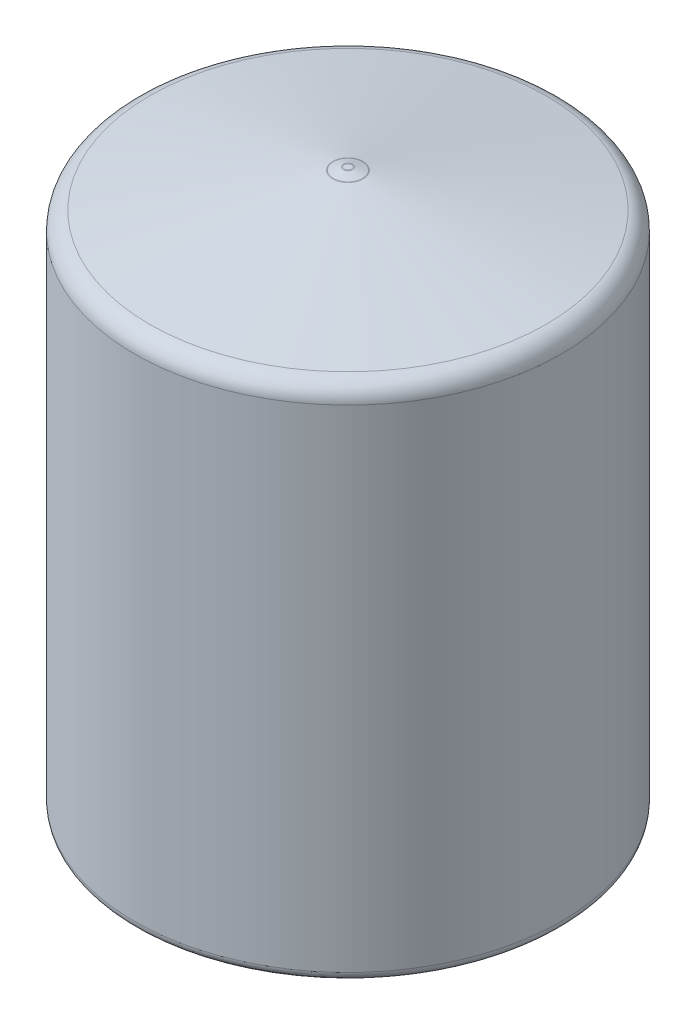
SolidWorks part; units mm, degrees
material "PE High Density"
ref_plane "Front Plane" through (0, 0, 0) normal (0, 0, 1) x (1, 0, 0)
ref_plane "Top Plane" through (0, 0, 0) normal (0, 1, 0) x (1, 0, 0)
ref_plane "Right Plane" through (0, 0, 0) normal (1, 0, 0) x (0, 0, -1)
sketch "Sketch1" plane through (0, 0, 0) normal (0, 0, 1) x (1, 0, 0)
  line L0 (10, 0) -> (10, 26.5856)
  line L1 (10.6855, 27.9826) -> (0.8, 29.849)
  line L2 (11.5, 0) -> (11.5, 27)
  line L3 (0, 30) -> (0, 29.5)
  line L4 (10, 26.5856) -> (1.2654, 28.2346)
  line L5 (0.2509, 29.9934) -> (0.8, 29.849)
  line L6 (0.2, 30) -> (0, 30)
  line L7 (10, 0) -> (11.5, 0)
  line L8 (0, 9.5) -> (0, 0) construction
  line L9 (0, 29.5) -> (1.2654, 28.2346)
  line L10 (0, 30) -> (-6.88, 27.1682) construction
  line L11 (0.1592, 28.4434) -> (-6.3091, 25.7811) construction
  line L12 (11.5, 27.8289) -> (0, 30) construction
  line L13 (10, 26.5856) -> (0.1592, 28.4434) construction
  line L14 (11.5, 0) -> (11.5, 27.8289) construction
  arc A0 (11.5, 27) -> (10.6855, 27.9826) centre (10.5, 27) ccw
  arc A1 (0.2509, 29.9934) -> (0.2, 30) centre (0.2, 29.8) ccw
  point P12 (0.794, 29.8501)
  point P22 (0, 0)
  point P23 (0, 0)
  point P24 (0, 0)
  point P25 (1.1903, 29.8)
  point P26 (0.7827, 29.8501)
  dimension "D5" = 1
  dimension "D3" = 0.2
  dimension "D1" = 1.5
  dimension "D2" = 23
  dimension "D4" = 30
  dimension "D6" = 27
  dimension "D7" = 0.5
  dimension "D8" = 0.2
  dimension "D9" = 45
  dimension "D10" = 0.8
revolve "Revolve1" add sketch "Sketch1" angle 360 about L8
fillet "Fillet1" radius 0.5 3 edges at (0, 0, -10) (0, 0, -11.5) (0, 29.849, -0.8)
